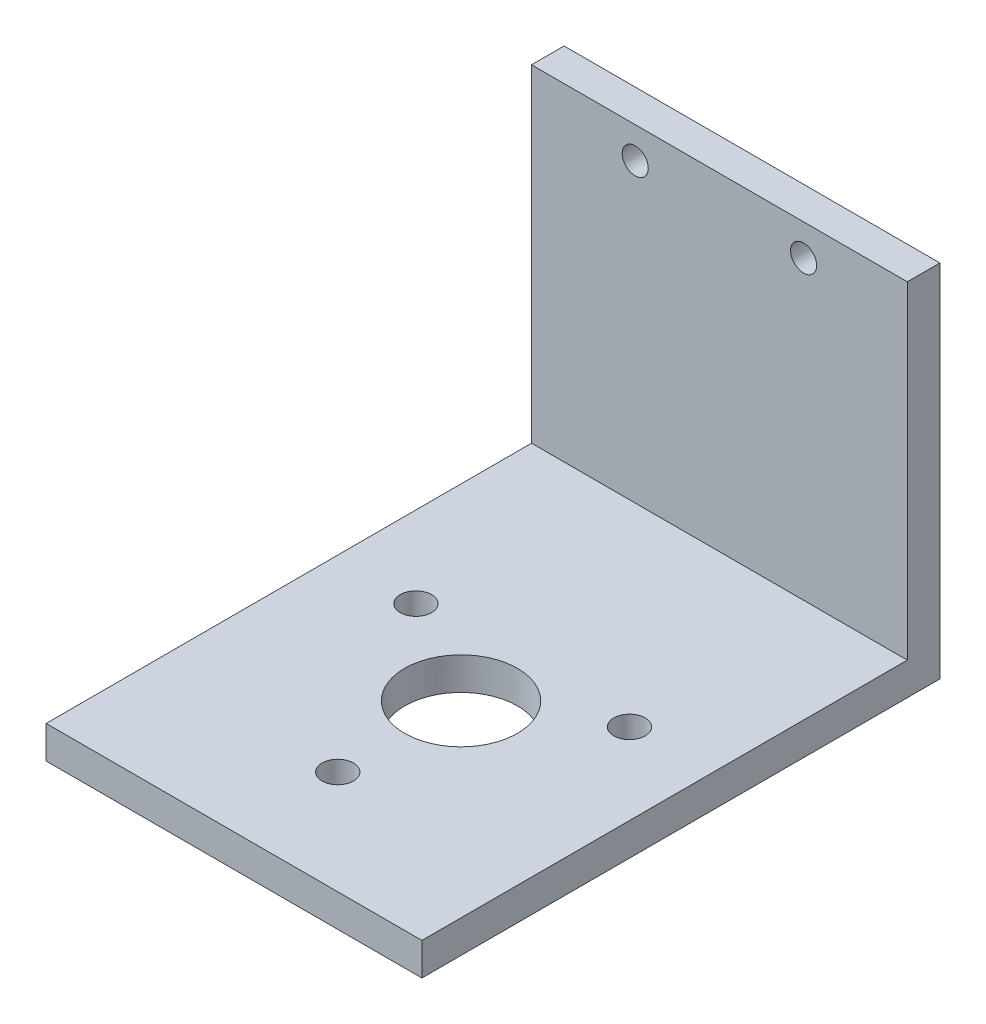
SolidWorks part; units mm, degrees
ref_plane "Front Plane" through (0, 0, 0) normal (0, 0, 1) x (1, 0, 0)
ref_plane "Top Plane" through (0, 0, 0) normal (0, 1, 0) x (1, 0, 0)
ref_plane "Right Plane" through (0, 0, 0) normal (1, 0, 0) x (0, 0, -1)
sketch "Sketch1" plane through (0, 0, 0) normal (0, 0, 1) x (1, 0, 0)
  line L0 (38.1, 73.0504) -> (38.1, -48.7301) construction
  line L1 (0, 0) -> (76.2, 0)
  line L2 (0, 0) -> (0, 73.0504)
  line L3 (0, 73.0504) -> (76.2, 73.0504)
  line L4 (76.2, 0) -> (76.2, 73.0504)
  circle A0 centre (21.0312, 66.7004) radius 2.6416
  circle A1 centre (55.1688, 66.7004) radius 2.6416
  dimension "D2" = 5.2832
  dimension "D1" = 76.2
  dimension "D3" = 21.0312
  dimension "D4" = 6.35
  dimension "D5" = 66.7004
extrude "Boss-Extrude1" add sketch "Sketch1" against normal blind 6.604
sketch "Sketch2" plane through (0, 0, 0) normal (0, 0, 1) x (1, 0, 0)
  line L0 (0, 73.0504) -> (0, 0) construction
  line L1 (0, 6.604) -> (76.2, 6.604)
  line L2 (0, 6.604) -> (0, 0)
  line L3 (0, 0) -> (76.2, 0)
  line L4 (76.2, 6.604) -> (76.2, 0)
  dimension "D1" = 6.604
extrude "Boss-Extrude2" add sketch "Sketch2" along normal blind 98.425
sketch "Sketch3" plane through (0, 6.604, 0) normal (0, 1, 0) x (1, 0, 0)
  line L0 (76.2, 0) -> (0, 0) construction
  line L1 (0, -98.425) -> (0, 0) construction
  circle A0 centre (38.1, -52.3875) radius 11.43
  circle A1 centre (38.1, -77.3875) radius 3.175
  circle A2 centre (16.4494, -39.8875) radius 3.175
  circle A3 centre (59.7506, -39.8875) radius 3.175
  point P14 (38.1, -52.3875)
  dimension "D2" = 22.86
  dimension "D3" = 6.35
  dimension "D1" = 52.3875
  dimension "D4" = 25
  dimension "D5" = 38.1
  dimension "D6" = 38.1
  dimension "D7" = 3
extrude "Cut-Extrude1" cut sketch "Sketch3" against normal blind 76.2
